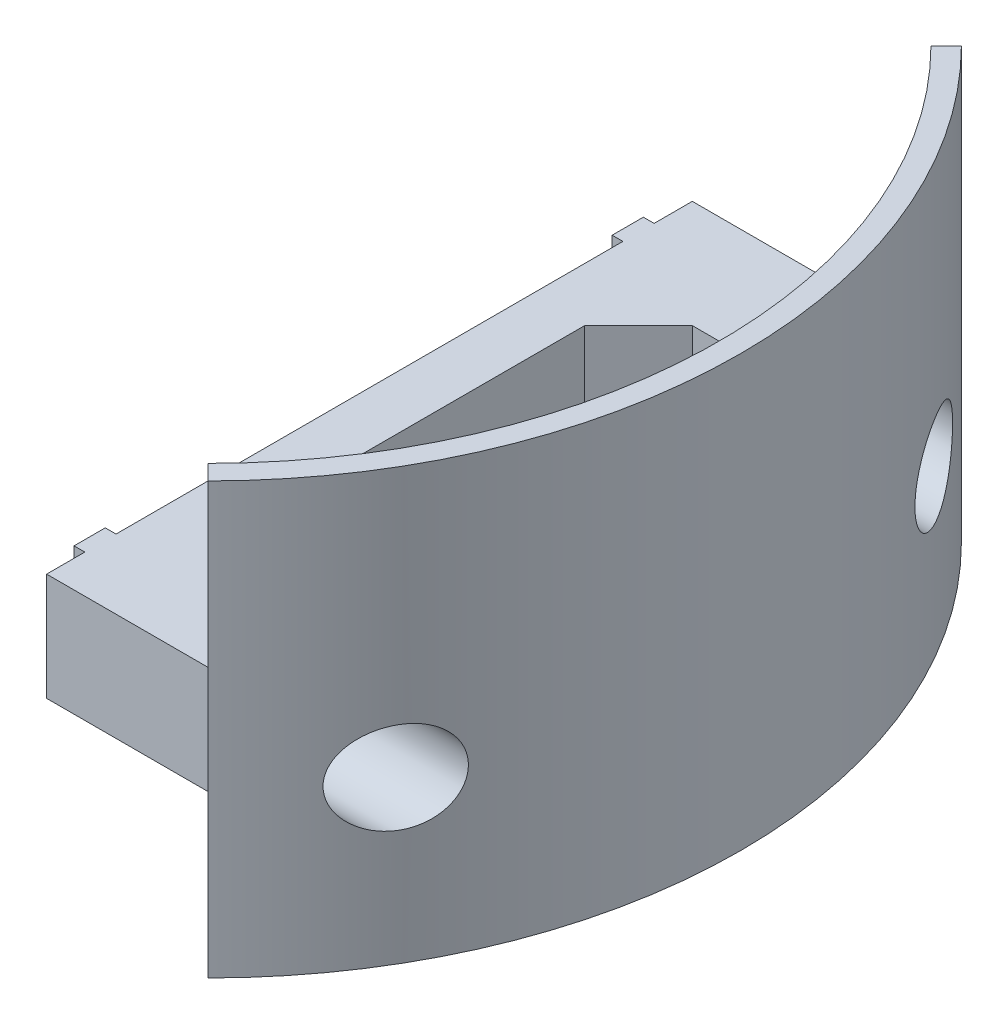
SolidWorks part; units mm, degrees
ref_plane "Front Plane" through (0, 0, 0) normal (0, 0, 1) x (1, 0, 0)
ref_plane "Top Plane" through (0, 0, 0) normal (0, 1, 0) x (1, 0, 0)
ref_plane "Right Plane" through (0, 0, 0) normal (1, 0, 0) x (0, 0, -1)
ref_axis "Axis1" through (0, -0.2847, 0) along (0, 1, 0)
ref_plane "SupportPlain" through (0, 10, 0) normal (0, 1, 0) x (1, 0, 0)
sketch "Sketch1" plane through (0, 0, 0) normal (0, 0, 1) x (1, 0, 0)
  line L0 (49.5, 0) -> (49.5, 40)
  line L5 (49.5, 40) -> (47.5, 40)
  line L6 (47.5, 40) -> (47.5, 0)
  line L7 (47.5, 0) -> (49.5, 0)
  point P9 (48.5, 0)
  dimension "D1" = 40
  dimension "D2" = 2
  dimension "D3" = 49.5
revolve "Main" add sketch "Sketch1" angle 90 mid plane about axis through (0, -0.2847, 0) along (0, 1, 0)
sketch "Sketch2" plane through (0, 10, 0) normal (0, -1, 0) x (-1, 0, 0)
  line L0 (-43.0842, -20) -> (-20, -20)
  line L1 (-36.8273, -30) -> (-15, -30)
  line L2 (-33.5876, -33.5876) -> (-33.5876, 33.5876) construction
  line L9 (-43.0842, 20) -> (-20, 20)
  line L10 (-15, -30) -> (-15, 30)
  line L11 (-15, 30) -> (-36.8273, 30)
  line L13 (-20, 20) -> (-20, -20)
  arc A0 (-43.0842, 20) -> (-36.8273, 30) centre (0, 0) cw
  circle A1 centre (0, 0) radius 50 construction
  arc A2 (-36.8273, -30) -> (-43.0842, -20) centre (0, 0) cw
  circle A3 centre (0, 0) radius 47.5 construction
  point P4 (0, 0)
  point P7 (0, 0)
  point P26 (-15, 0)
  dimension "D7" = 10
  dimension "D4" = 100
  dimension "D1" = 10
  dimension "D2" = 15
  dimension "D3" = 5
  dimension "D8" = 40
extrude "Support" add sketch "Sketch2" against normal blind 10
sketch "Sketch6" plane through (0, 10, 0) normal (0, 1, 0) x (1, 0, 0)
  line L0 (15, -30) -> (15, 30) construction
  line L1 (14, -23.55) -> (15, -23.55)
  line L2 (14, -23.55) -> (14, -26.45)
  line L3 (14, -26.45) -> (15, -26.45)
  line L4 (15, -23.55) -> (15, -26.45)
  line L6 (14, 26.45) -> (15, 26.45)
  line L7 (14, 26.45) -> (14, 23.55)
  line L8 (14, 23.55) -> (15, 23.55)
  line L9 (15, 26.45) -> (15, 23.55)
  line L11 (15, -30) -> (15, 30) construction
  point P10 (15, -30)
  point P13 (15, 30)
  dimension "D1" = 3.55
  dimension "D2" = 2.9
  dimension "D3" = 1
  dimension "D4" = 3.55
extrude "Fix" add sketch "Sketch6" along normal up to surface (10 mm away) up to face at (28.8058, 20, 0)
sketch "Sketch9" plane through (20, 0, 0) normal (1, 0, 0) x (0, 0, -1)
  line L0 (26.45, 10) -> (23.55, 10) construction
  line L1 (30, 20) -> (30, 10) construction
  line L2 (-30, 20) -> (-30, 10) construction
  circle A0 centre (25, 15) radius 1.6
  circle A1 centre (-25, 15) radius 1.6
  dimension "D1" = 3.2
  dimension "D2" = 3.2
  dimension "D3" = 5
  dimension "D4" = 5
  dimension "D5" = 5
extrude "Holes" cut sketch "Sketch9" against normal through all
sketch "Sketch10" plane through (20, 0, 0) normal (1, 0, 0) x (0, 0, -1)
  circle A0 centre (25, 15) radius 4.25
  circle A1 centre (-25, 15) radius 4.25
  arc A2 (23.55, 14.3236) -> (26.45, 14.3236) centre (25, 15) ccw construction
  arc A3 (-26.45, 14.3236) -> (-23.55, 14.3236) centre (-25, 15) ccw construction
  dimension "D1" = 8.5
extrude "BigHoles" cut sketch "Sketch10" along normal through all
sketch "Sketch11" plane through (0, 20, 0) normal (0, 1, 0) x (1, 0, 0)
  line L0 (20, 20) -> (25, 20)
  line L1 (43.0842, 20) -> (20, 20) construction
  line L2 (25, 20) -> (20, 15)
  line L3 (20, 20) -> (20, -20) construction
  line L4 (20, 15) -> (20, 20)
  line L5 (20, -20) -> (20, -15)
  line L6 (20, -15) -> (25, -20)
  line L7 (20, -20) -> (43.0842, -20) construction
  line L8 (25, -20) -> (20, -20)
  line L9 (40.2797, 20) -> (45.2797, 20)
  line L10 (45.2797, 20) -> (45.2797, 15)
  line L11 (45.2797, 15) -> (40.2797, 20)
  line L12 (40.2797, -20) -> (45.2797, -20)
  line L13 (45.2797, -20) -> (45.2797, -14.3527)
  line L14 (45.2797, -14.3527) -> (40.2797, -20)
  arc A0 (35.0018, -35.0018) -> (35.0018, 35.0018) centre (0, 0) ccw construction
  arc A1 (33.5876, -33.5876) -> (33.5876, 33.5876) centre (0, 0) ccw construction
  point P22 (0, 0)
  dimension "D1" = 5
  dimension "D2" = 5
  dimension "D3" = 5
extrude "Boss-Extrude3" add sketch "Sketch11" against normal blind 10
